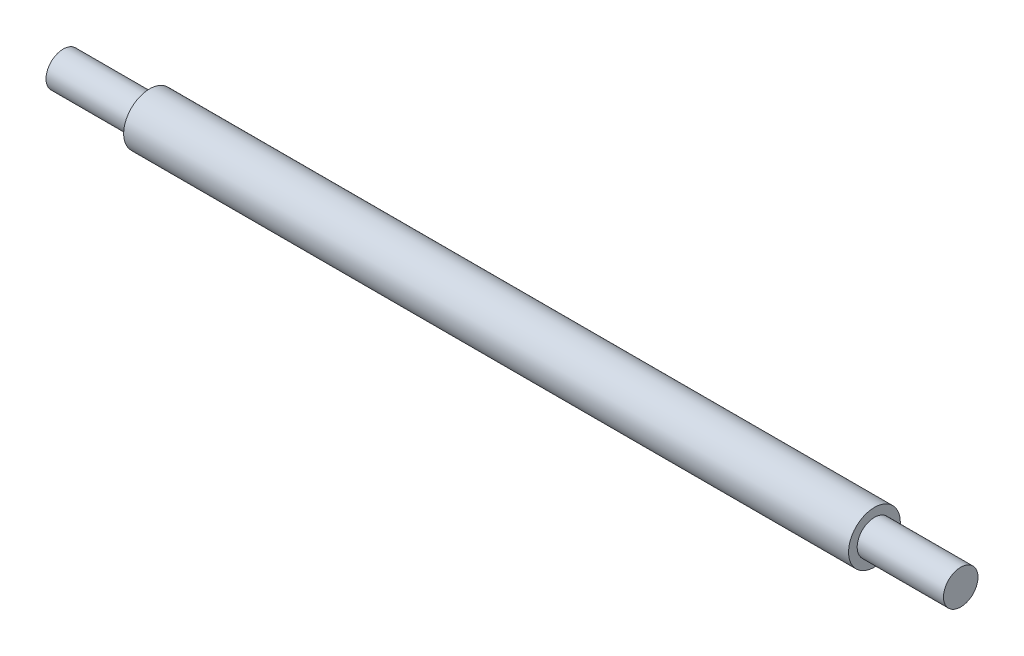
SolidWorks part; units mm, degrees
ref_plane "Front Plane" through (0, 0, 0) normal (0, 0, 1) x (1, 0, 0)
ref_plane "Top Plane" through (0, 0, 0) normal (0, 1, 0) x (1, 0, 0)
ref_plane "Right Plane" through (0, 0, 0) normal (1, 0, 0) x (0, 0, -1)
sketch "Sketch1" plane through (0, 0, 0) normal (1, 0, 0) x (0, 0, -1)
  circle A0 centre (0, 0) radius 3
  dimension "D1" = 6
extrude "Boss-Extrude1" add sketch "Sketch1" along normal blind 84
sketch "Sketch2" plane through (84, 0, 0) normal (1, 0, 0) x (0, 0, -1)
  circle A0 centre (0, 0) radius 2
extrude "Boss-Extrude2" add sketch "Sketch2" along normal blind 10
sketch "Sketch3" plane through (0, 0, 0) normal (-1, 0, 0) x (0, 0, 1)
  circle A0 centre (0, 0) radius 2
extrude "Boss-Extrude3" add sketch "Sketch3" along normal blind 10
